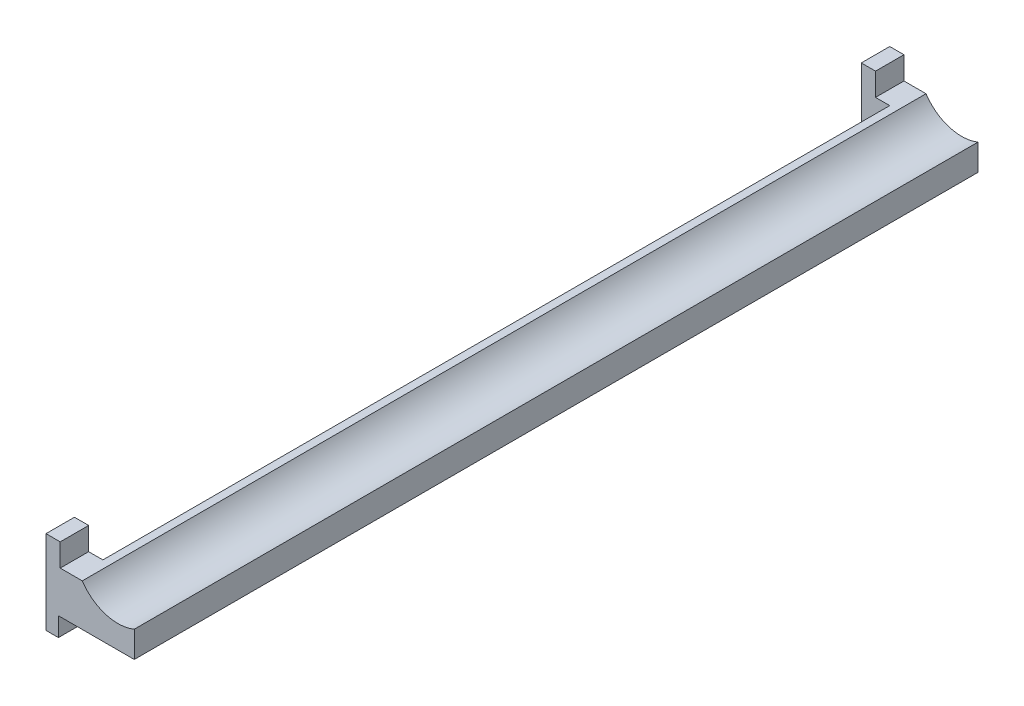
SolidWorks part; units mm, degrees
ref_plane "Front Plane" through (0, 0, 0) normal (0, 0, 1) x (1, 0, 0)
ref_plane "Top Plane" through (0, 0, 0) normal (0, 1, 0) x (1, 0, 0)
ref_plane "Right Plane" through (0, 0, 0) normal (1, 0, 0) x (0, 0, -1)
sketch "Sketch1" plane through (0, 0, 0) normal (0, 0, 1) x (1, 0, 0)
  line L0 (0, 0) -> (187.42, 0) construction
  line L1 (0, 138.5306) -> (0, -235.9813) construction
  line L2 (187.42, 0) -> (225.3, 0) construction
  line L15 (187.42, 44.22) -> (187.42, -44.22)
  line L16 (187.42, -44.22) -> (200.5188, -44.22)
  line L17 (200.5188, -44.22) -> (200.5188, -24.22)
  line L18 (200.5188, -24.22) -> (280.5188, -24.22)
  line L19 (280.5188, -24.22) -> (280.5188, 3.4454)
  line L21 (202.42, 20.22) -> (202.42, 44.22)
  line L22 (187.42, 44.22) -> (202.42, 44.22)
  line L23 (263.25, 0) -> (263.25, 45) construction
  line L24 (225.6874, 20.22) -> (202.42, 20.22)
  arc A2 (225.6874, 20.22) -> (280.5188, 3.4454) centre (263.25, 45) ccw
  dimension "D1" = 187.42
  dimension "D7" = 44.22
  dimension "D3" = 263.25
extrude "Boss-Extrude1" add sketch "Sketch1" against normal blind 890
sketch "Sketch2" plane through (187.42, 0, 0) normal (-1, 0, 0) x (0, 0, 1)
  line L1 (-890, 44.22) -> (0, 44.22) construction
  line L2 (-860, 44.22) -> (-860, -44.22)
  line L3 (-890, -44.22) -> (0, -44.22) construction
  line L4 (-860, -44.22) -> (-30, -44.22)
  line L5 (-30, -44.22) -> (-30, 44.22)
  line L6 (-30, 44.22) -> (-860, 44.22)
  line L7 (0, 44.22) -> (0, -44.22) construction
  dimension "D1" = 30
extrude "Cut-Extrude1" cut sketch "Sketch2" against normal blind 30
